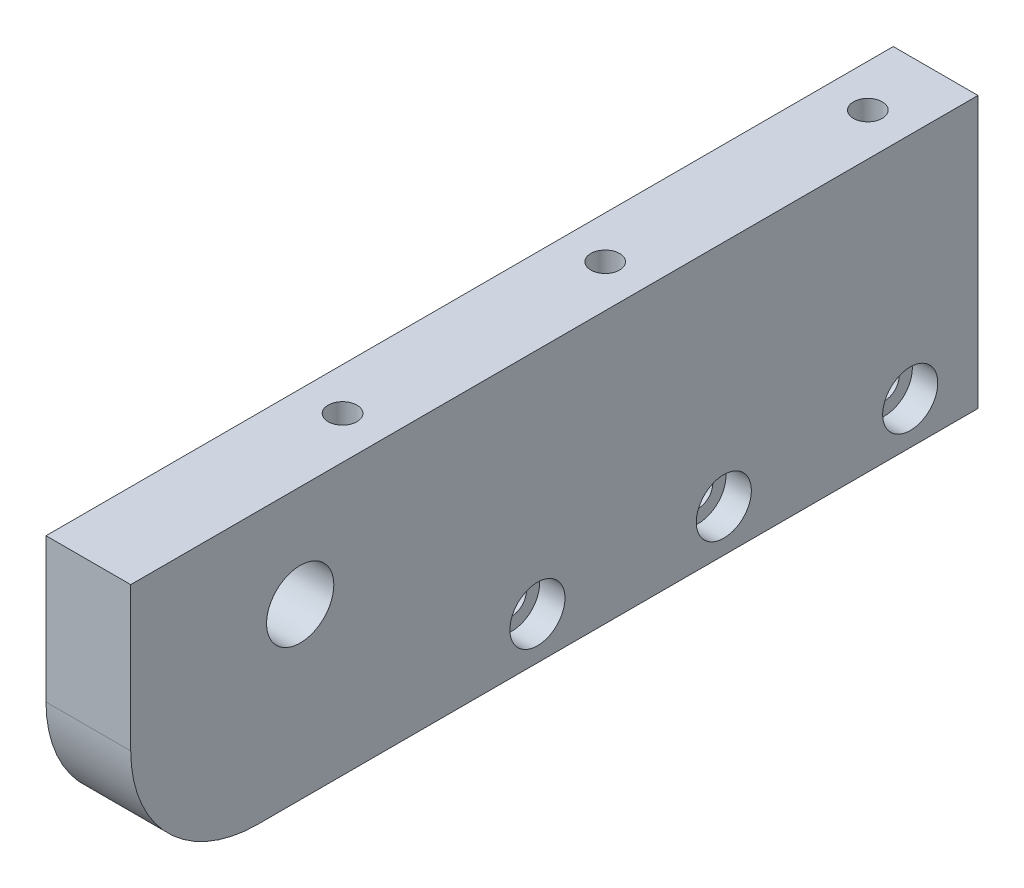
SolidWorks part; units mm, degrees
material "Plain Carbon Steel"
ref_plane "Front Plane" through (0, 0, 0) normal (0, 0, 1) x (1, 0, 0)
ref_plane "Top Plane" through (0, 0, 0) normal (0, 1, 0) x (1, 0, 0)
ref_plane "Right Plane" through (0, 0, 0) normal (1, 0, 0) x (0, 0, -1)
sketch "Sketch1" plane through (0, 0, 0) normal (1, 0, 0) x (0, 0, -1)
  line L1 (-50, -16) -> (50, -16)
  line L2 (-50, -16) -> (-50, 16)
  line L3 (-50, 16) -> (50, 16)
  line L4 (50, -16) -> (50, 16)
  line L5 (-50, -16) -> (50, 16) construction
  line L6 (-50, 16) -> (50, -16) construction
  circle A0 centre (-30, 4) radius 3.9688
  point P0 (0, 0)
  dimension "D3" = 7.9375
  dimension "D1" = 32
  dimension "D2" = 100
  dimension "D4" = 20
  dimension "D5" = 12
extrude "Boss-Extrude1" add sketch "Sketch1" along normal blind 10
fillet "Fillet1" radius 15 1 edges at (5, -16, 50)
hole_wizard "CBORE for M3 SHCS" positions "Sketch4" profile "Sketch5" counterbore size "M3" standard "ANSI Metric"
sketch "Sketch4" plane through (-726.2935, 26, -1323.2827) normal (0, 1, 0) x (1, 0, 0)
  line L3 (621.2935, -1281.2827) -> (621.2935, -1365.2827) construction
  line L5 (731.2935, -1281.2827) -> (731.2935, -1343.2827) construction
  circle A0 centre (731.2935, -1281.2827) radius 2.243
  circle A1 centre (731.2935, -1343.2827) radius 2.2384
  circle A3 centre (621.2935, -1281.2827) radius 2.3325
  circle A4 centre (621.2935, -1365.2827) radius 1.7576
  circle A5 centre (621.2935, -1323.2827) radius 1.8624
  circle A6 centre (731.2935, -1312.2827) radius 2.0271
  point P1 (731.2935, -1281.2827)
  point P8 (731.2935, -1343.2827)
  point P15 (621.2935, -1281.2827)
  point P17 (621.2935, -1365.2827)
  point P19 (621.2935, -1323.2827)
  point P27 (731.2935, -1312.2827)
sketch "Sketch5" plane through (5, 26, -42) normal (1, 0, 0) x (0, 0, 1)
  line L0 (0, 0) -> (0, 24.0215)
  line L1 (0, 24.0215) -> (1.7, 23)
  line L2 (1.7, 23) -> (1.7, 3)
  line L3 (1.7, 3) -> (3.25, 3)
  line L4 (3.25, 3) -> (3.25, 0)
  line L5 (3.25, 0) -> (0, 0)
  line L6 (0, 24.0215) -> (-1.7, 23) construction
  line L7 (0, -6.35) -> (0, 107.95) construction
  dimension "Hole Dia." = 3.4
  dimension "Hole Depth" = 23
  dimension "C'Bore Dia." = 6.5
  dimension "C'Bore Depth" = 3
  dimension "Drill Angle" = 118
hole_wizard "CBORE for M3 SHCS1" positions "Sketch6" profile "Sketch7" counterbore size "M3" standard "ANSI Metric"
sketch "Sketch6" plane through (10, -904.0121, -1323.2827) normal (1, 0, 0) x (0, 0, -1)
  line L0 (-1281.2827, 893.0121) -> (-1325.2827, 893.0121) construction
  point P0 (-1281.2827, 893.0121)
  point P1 (-1325.2827, 893.0121)
  point P9 (-1303.2827, 893.0121)
sketch "Sketch7" plane through (10, -11, -42) normal (0, 1, 0) x (0, 0, -1)
  line L0 (0, 0) -> (0, 24.0215)
  line L1 (0, 24.0215) -> (1.7, 23)
  line L2 (1.7, 23) -> (1.7, 3)
  line L3 (1.7, 3) -> (3.25, 3)
  line L4 (3.25, 3) -> (3.25, 0)
  line L5 (3.25, 0) -> (0, 0)
  line L6 (0, 24.0215) -> (-1.7, 23) construction
  line L7 (0, -6.35) -> (0, 107.95) construction
  dimension "Hole Dia." = 3.4
  dimension "Hole Depth" = 23
  dimension "C'Bore Dia." = 6.5
  dimension "C'Bore Depth" = 3
  dimension "Drill Angle" = 118
